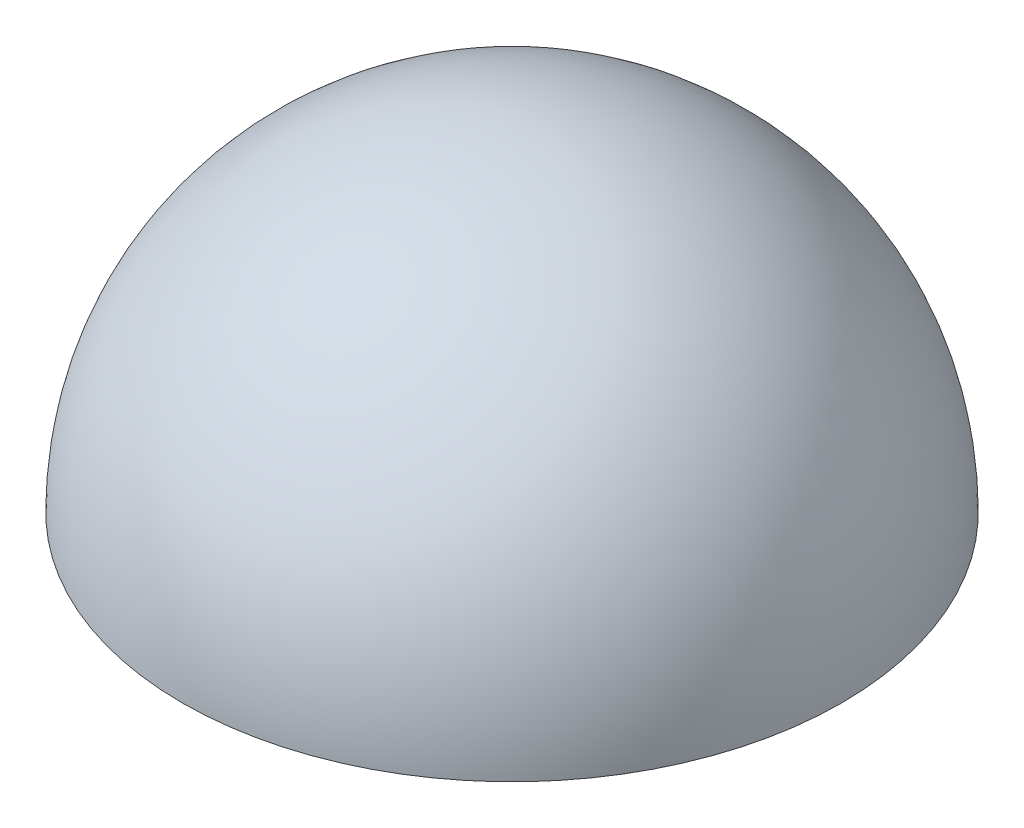
SolidWorks part; units mm, degrees
ref_plane "Front Plane" through (0, 0, 0) normal (0, 0, 1) x (1, 0, 0)
ref_plane "Top Plane" through (0, 0, 0) normal (0, 1, 0) x (1, 0, 0)
ref_plane "Right Plane" through (0, 0, 0) normal (1, 0, 0) x (0, 0, -1)
sketch "Sketch1" plane through (0, 0, 0) normal (0, 0, 1) x (1, 0, 0)
  line L0 (-11, 0) -> (-12.2, 0)
  line L2 (0, 0) -> (0, 15.033) construction
  line L3 (0, 12.2) -> (0, 11)
  arc A0 (-11, 0) -> (0, 11) centre (0, 0) cw
  arc A1 (-12.2, 0) -> (0, 12.2) centre (0, 0) cw
  dimension "D1" = 11
  dimension "D2" = 12.2
revolve "Revolve2" add sketch "Sketch1" angle 360 about L2
equation "\"dia_difflayer\"= 13"
equation "\"dia_outer_out\"= 12.5"
equation "\"dia_outer_in\"= 12"
equation "\"dia_inner_out\"= 11"
equation "\"dia_inner_in\"= 10.5"
equation "\"degrees\"= 12.5"
equation "\"d_marker\"= 1"
equation "\"t_marker\"= 0.5"
equation "\"n_markers_1\"= 6"
equation "\"n_markers_2\"= round ( 6 * sin ( 2*\"degrees\" ) / sin ( \"degrees\" ) )"
equation "\"n_markers_3\"= round ( 6 * sin ( 3*\"degrees\" ) / sin ( \"degrees\" ) )"
equation "\"n_markers_4\"= round ( 6 * sin ( 4*\"degrees\" ) / sin ( \"degrees\" ) )"
equation "\"n_markers_5\"= round ( 6 * sin ( 5*\"degrees\" ) / sin ( \"degrees\" ) )"
equation "\"n_teeth\"= 8"
